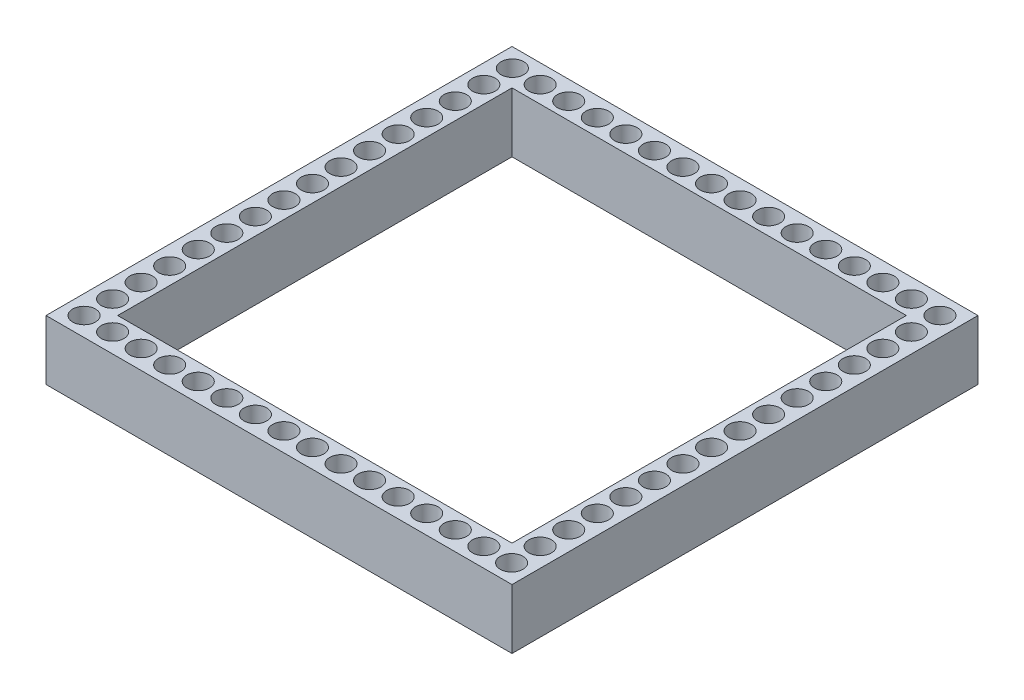
SolidWorks part; units mm, degrees
material "PP Copolymer"
ref_plane "Front Plane" through (0, 0, 0) normal (0, 0, 1) x (1, 0, 0)
ref_plane "Top Plane" through (0, 0, 0) normal (0, 1, 0) x (1, 0, 0)
ref_plane "Right Plane" through (0, 0, 0) normal (1, 0, 0) x (0, 0, -1)
sketch "Sketch2" plane through (0, 0, 0) normal (0, 1, 0) x (1, 0, 0)
  line L1 (-19.5, 19.5) -> (19.5, 19.5)
  line L2 (-19.5, 19.5) -> (-19.5, -19.5)
  line L3 (-19.5, -19.5) -> (19.5, -19.5)
  line L4 (19.5, 19.5) -> (19.5, -19.5)
  line L5 (-19.5, 19.5) -> (19.5, -19.5) construction
  line L6 (-19.5, -19.5) -> (19.5, 19.5) construction
  line L7 (-16.5, 16.5) -> (16.5, 16.5)
  line L8 (-16.5, 16.5) -> (-16.5, -16.5)
  line L9 (-16.5, -16.5) -> (16.5, -16.5)
  line L10 (16.5, 16.5) -> (16.5, -16.5)
  line L11 (-16.5, 16.5) -> (16.5, -16.5) construction
  line L12 (-16.5, -16.5) -> (16.5, 16.5) construction
  point P0 (0, 0)
  point P6 (0, 0)
  point P11 (0, 0)
extrude "Boss-Extrude1" add sketch "Sketch2" along normal blind 5
sketch "Sketch1" plane through (0, 0, 0) normal (0, 1, 0) x (1, 0, 0)
  circle A0 centre (-17.909, -17.909) radius 0.95
  circle A1 centre (-15.519, -17.909) radius 0.95
  circle A2 centre (-13.129, -17.909) radius 0.95
  circle A3 centre (-10.739, -17.909) radius 0.95
  circle A4 centre (-8.349, -17.909) radius 0.95
  circle A5 centre (-5.959, -17.909) radius 0.95
  circle A6 centre (-3.569, -17.909) radius 0.95
  circle A7 centre (-1.179, -17.909) radius 0.95
  circle A8 centre (1.211, -17.909) radius 0.95
  circle A9 centre (3.601, -17.909) radius 0.95
  circle A10 centre (5.991, -17.909) radius 0.95
  circle A11 centre (8.381, -17.909) radius 0.95
  circle A12 centre (10.771, -17.909) radius 0.95
  circle A13 centre (13.161, -17.909) radius 0.95
  circle A14 centre (15.551, -17.909) radius 0.95
  circle A16 centre (17.909, 17.909) radius 0.95
  circle A17 centre (17.909, -17.941) radius 0.95
  circle A18 centre (17.909, -15.551) radius 0.95
  circle A19 centre (17.909, -13.161) radius 0.95
  circle A20 centre (17.909, -10.771) radius 0.95
  circle A21 centre (17.909, -8.381) radius 0.95
  circle A22 centre (17.909, -5.991) radius 0.95
  circle A23 centre (17.909, -3.601) radius 0.95
  circle A24 centre (17.909, -1.211) radius 0.95
  circle A25 centre (17.909, 1.179) radius 0.95
  circle A26 centre (17.909, 3.569) radius 0.95
  circle A27 centre (17.909, 5.959) radius 0.95
  circle A28 centre (17.909, 8.349) radius 0.95
  circle A29 centre (17.909, 10.739) radius 0.95
  circle A30 centre (17.909, 13.129) radius 0.95
  circle A31 centre (17.909, 15.519) radius 0.95
  circle A32 centre (15.519, 17.909) radius 0.95
  circle A33 centre (13.129, 17.909) radius 0.95
  circle A34 centre (10.739, 17.909) radius 0.95
  circle A35 centre (8.349, 17.909) radius 0.95
  circle A36 centre (5.959, 17.909) radius 0.95
  circle A37 centre (3.569, 17.909) radius 0.95
  circle A38 centre (1.179, 17.909) radius 0.95
  circle A39 centre (-1.211, 17.909) radius 0.95
  circle A40 centre (-3.601, 17.909) radius 0.95
  circle A41 centre (-5.991, 17.909) radius 0.95
  circle A42 centre (-8.381, 17.909) radius 0.95
  circle A43 centre (-10.771, 17.909) radius 0.95
  circle A44 centre (-13.161, 17.909) radius 0.95
  circle A45 centre (-15.551, 17.909) radius 0.95
  circle A47 centre (-17.909, 17.941) radius 0.95
  circle A48 centre (-17.909, 15.551) radius 0.95
  circle A49 centre (-17.909, 13.161) radius 0.95
  circle A50 centre (-17.909, 10.771) radius 0.95
  circle A51 centre (-17.909, 8.381) radius 0.95
  circle A52 centre (-17.909, 5.991) radius 0.95
  circle A53 centre (-17.909, 3.601) radius 0.95
  circle A54 centre (-17.909, 1.211) radius 0.95
  circle A55 centre (-17.909, -1.179) radius 0.95
  circle A56 centre (-17.909, -3.569) radius 0.95
  circle A57 centre (-17.909, -5.959) radius 0.95
  circle A58 centre (-17.909, -8.349) radius 0.95
  circle A59 centre (-17.909, -10.739) radius 0.95
  circle A60 centre (-17.909, -13.129) radius 0.95
  circle A61 centre (-17.909, -15.519) radius 0.95
  circle A62 centre (17.941, -17.909) radius 0.95 [skipped]
  point P0 (0, 0)
  dimension "D1" = 16
extrude "Cut-Extrude1" cut sketch "Sketch1" along normal through all
